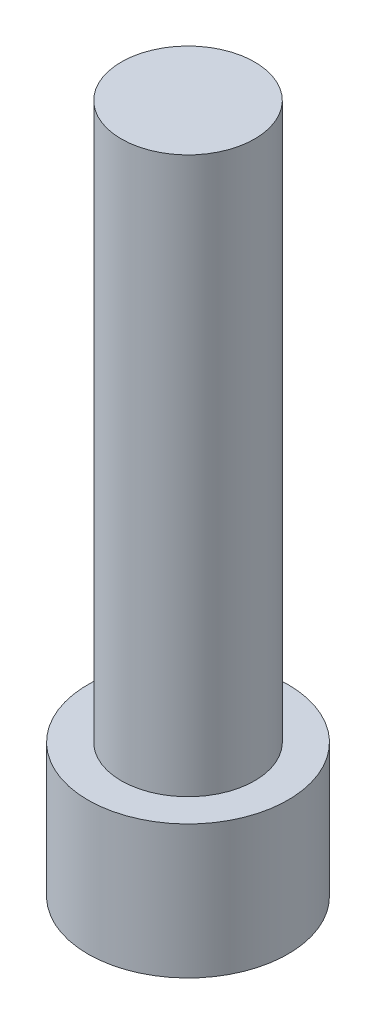
SolidWorks part; units mm, degrees
ref_plane "Front Plane" through (0, 0, 0) normal (0, 0, 1) x (1, 0, 0)
ref_plane "Top Plane" through (0, 0, 0) normal (0, 1, 0) x (1, 0, 0)
ref_plane "Right Plane" through (0, 0, 0) normal (1, 0, 0) x (0, 0, -1)
sketch "Sketch1" plane through (0, 0, 0) normal (0, 1, 0) x (1, 0, 0)
  circle A0 centre (0, 0) radius 9
extrude "Boss-Extrude1" add sketch "Sketch1" along normal blind 12
sketch "Sketch2" plane through (0, 12, 0) normal (0, 1, 0) x (1, 0, 0)
  circle A0 centre (0, 0) radius 6
extrude "Boss-Extrude2" add sketch "Sketch2" along normal blind 50
